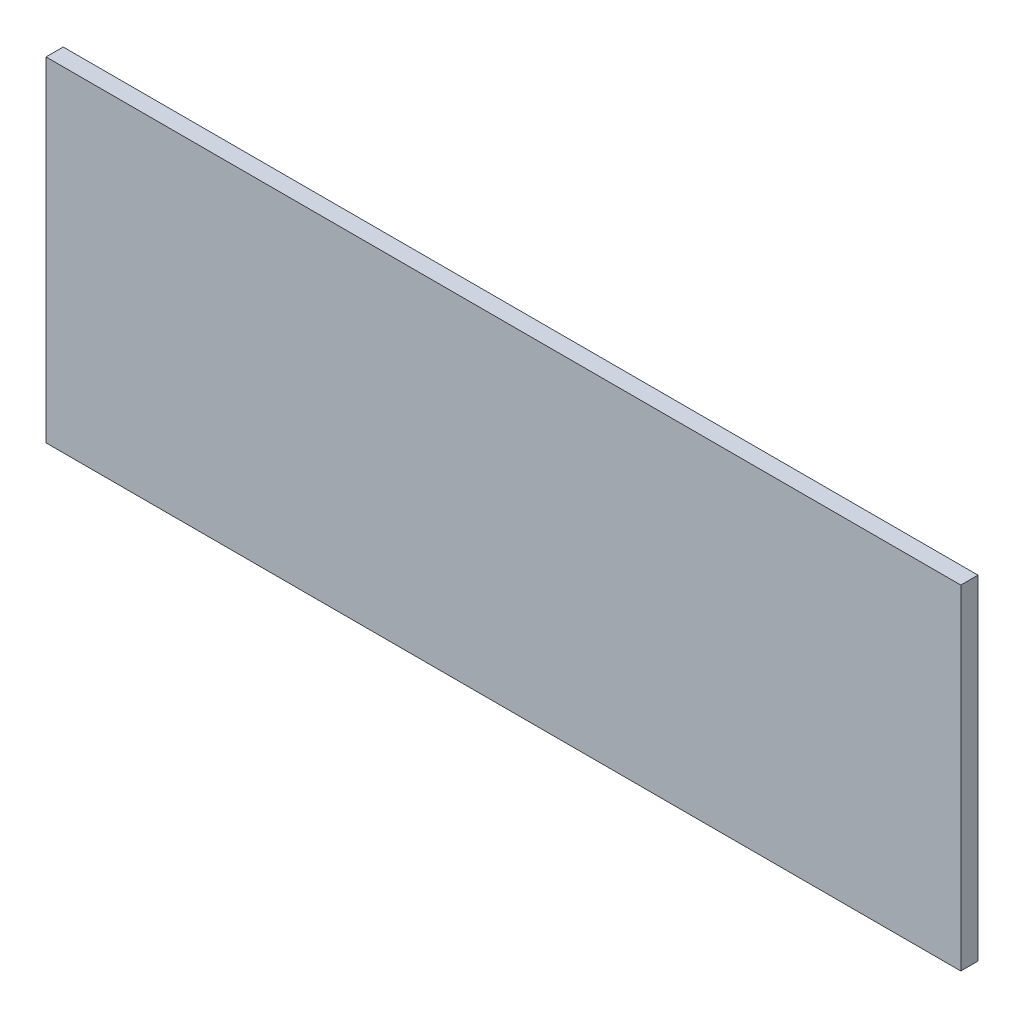
SolidWorks part; units mm, degrees
ref_plane "Front Plane" through (0, 0, 0) normal (0, 0, 1) x (1, 0, 0)
ref_plane "Top Plane" through (0, 0, 0) normal (0, 1, 0) x (1, 0, 0)
ref_plane "Right Plane" through (0, 0, 0) normal (1, 0, 0) x (0, 0, -1)
sketch "Sketch1" plane through (0, 0, 0) normal (0, 0, 1) x (1, 0, 0)
  line L0 (0, 0) -> (266, 0)
  line L5 (0, 0) -> (0, -97.1922)
  line L6 (266, 0) -> (266, -97.1922)
  line L7 (0, -97.1922) -> (266, -97.1922)
  dimension "D1" = 266
  dimension "D2" = 97.1922
extrude "Boss-Extrude1" add sketch "Sketch1" along normal blind 5
